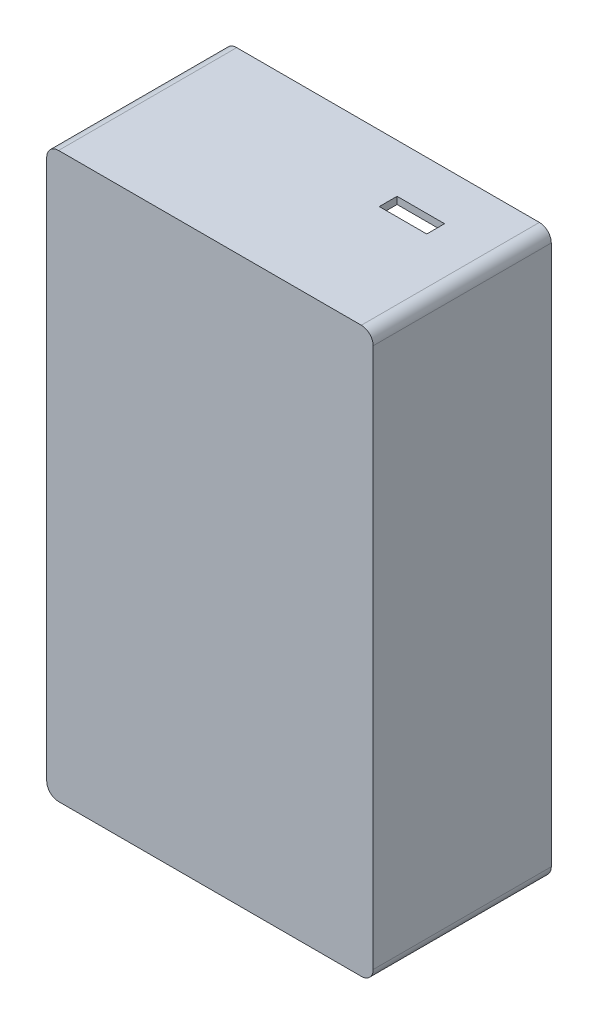
SolidWorks part; units mm, degrees
ref_plane "Front Plane" through (0, 0, 0) normal (0, 0, 1) x (1, 0, 0)
ref_plane "Top Plane" through (0, 0, 0) normal (0, 1, 0) x (1, 0, 0)
ref_plane "Right Plane" through (0, 0, 0) normal (1, 0, 0) x (0, 0, -1)
sketch "Sketch1" plane through (0, 0, 0) normal (0, 0, 1) x (1, 0, 0)
  line L1 (0, 0) -> (55, 0)
  line L2 (0, 0) -> (0, -95)
  line L3 (0, -95) -> (55, -95)
  line L4 (55, 0) -> (55, -95)
  dimension "D1" = 55
  dimension "D2" = 95
extrude "Boss-Extrude1" add sketch "Sketch1" along normal blind 30 contours L1 L4 L3 L2
sketch "Sketch2" plane through (0, 0, 0) normal (0, 0, -1) x (-1, 0, 0)
  line L0 (-55, 0) -> (-55, -95) construction
  line L1 (-53.8, -1.2) -> (-1.2, -1.2)
  line L2 (-53.8, -1.2) -> (-53.8, -93.8)
  line L3 (-53.8, -93.8) -> (-1.2, -93.8)
  line L4 (-1.2, -1.2) -> (-1.2, -93.8)
  line L5 (0, 0) -> (-55, 0) construction
  line L6 (0, 0) -> (0, -95) construction
  line L7 (0, -95) -> (-55, -95) construction
  dimension "D1" = 1.2
  dimension "D2" = 1.2
  dimension "D3" = 1.2
  dimension "D4" = 1.2
extrude "Cut-Extrude1" cut sketch "Sketch2" against normal offset from surface (28.8 mm away) 1.2 up to face at (27.5, -47.5, 30)
sketch "Sketch3" plane through (0, 0, 28.8) normal (0, 0, -1) x (-1, 0, 0)
  line L0 (-1.2, -93.8) -> (-1.2, -1.2) construction
  line L1 (-1.2, -1.2) -> (-53.8, -1.2) construction
  circle A0 centre (-4.2, -4.2) radius 3.5
  circle A1 centre (-48.2, -4.2) radius 3.5
  circle A2 centre (-48.2, -88.2) radius 3.5
  circle A3 centre (-4.2, -88.2) radius 3.5
  dimension "D1" = 7
  dimension "D2" = 3
  dimension "D6" = 44
  dimension "D3" = 3
  dimension "D7" = 84
  dimension "D4" = 2
  dimension "D5" = 2
extrude "Boss-Extrude2" add sketch "Sketch3" along normal blind 16
sketch "Sketch6" plane through (0, 0, 12.8) normal (0, 0, -1) x (-1, 0, 0)
  circle A0 centre (-4.2, -4.2) radius 1.6
  circle A1 centre (-4.2, -4.2) radius 3.5 construction
  circle A2 centre (-48.2, -4.2) radius 1.6
  circle A3 centre (-48.2, -4.2) radius 3.5 construction
  circle A4 centre (-48.2, -88.2) radius 1.6
  circle A5 centre (-48.2, -88.2) radius 3.5 construction
  circle A6 centre (-4.2, -88.2) radius 1.6
  circle A7 centre (-4.2, -88.2) radius 3.5 construction
  dimension "D1" = 3.2
  dimension "D2" = 3.2
  dimension "D3" = 3.2
  dimension "D4" = 3.2
extrude "Boss-Extrude3" add sketch "Sketch6" along normal blind 1.5
fillet "Fillet3" radius 2 4 edges at (0, 0, 15) (0, -95, 15) (55, -95, 15) (55, 0, 15)
sketch "Sketch7" plane through (0, 0, 11.3) normal (0, 0, -1) x (-1, 0, 0)
  circle A0 centre (-4.2, -4.2) radius 1.2
  circle A2 centre (-4.2, -4.2) radius 3.5 construction
  circle A3 centre (-48.2, -4.2) radius 1.2
  circle A4 centre (-48.2, -88.2) radius 1.2
  circle A5 centre (-4.2, -88.2) radius 1.2
  circle A6 centre (-4.2, -4.2) radius 1.6 construction
  dimension "D1" = 2.4
  dimension "D4" = 44
  dimension "D5" = 84
  dimension "D2" = 2
  dimension "D3" = 2
sketch "Sketch8" plane through (0, 0, 28.8) normal (0, 0, -1) x (-1, 0, 0)
  line L0 (-1.2, -1.2) -> (-2.3972, -1.2) construction
  line L1 (-53.8, -21.2) -> (-9.6, -21.2)
  line L2 (-53.8, -21.2) -> (-53.8, -53.6)
  line L3 (-53.8, -53.6) -> (-9.6, -53.6)
  line L4 (-9.6, -21.2) -> (-9.6, -53.6)
  line L5 (-53.8, -1.2) -> (-53.8, -93.8) construction
  dimension "D1" = 32.4
  dimension "D2" = 44.2
  dimension "D3" = 20
extrude "Boss-Extrude4" add sketch "Sketch8" along normal blind 10
sketch "Sketch9" plane through (0, 0, 18.8) normal (0, 0, -1) x (-1, 0, 0)
  line L0 (-9.6, -21.2) -> (-53.8, -21.2) construction
  line L1 (-53.8, -22.4) -> (-10.8, -22.4)
  line L2 (-53.8, -22.4) -> (-53.8, -52.4)
  line L3 (-53.8, -52.4) -> (-10.8, -52.4)
  line L4 (-10.8, -22.4) -> (-10.8, -52.4)
  line L5 (-53.8, -53.6) -> (-9.6, -53.6) construction
  line L6 (-9.6, -53.6) -> (-9.6, -21.2) construction
  line L8 (-53.8, -21.2) -> (-53.8, -53.6) construction
  dimension "D1" = 1.2
  dimension "D2" = 1.2
  dimension "D3" = 1.2
extrude "Cut-Extrude3" cut sketch "Sketch9" against normal blind 10
sketch "Sketch11" plane through (0, 0, 0) normal (0, 1, 0) x (1, 0, 0)
  line L1 (45.2, -11.18) -> (37.2, -11.18)
  line L2 (45.2, -11.18) -> (45.2, -8.18)
  line L3 (45.2, -8.18) -> (37.2, -8.18)
  line L4 (37.2, -11.18) -> (37.2, -8.18)
  line L8 (51.7, -12.8) -> (44.7, -12.8) construction
  dimension "D1" = 8
  dimension "D2" = 3
  dimension "D3" = 3
  dimension "D4" = 1.62
extrude "Cut-Extrude4" cut sketch "Sketch11" against normal up to next
extrude "Cut-Extrude5" cut sketch "Sketch7" against normal blind 16
